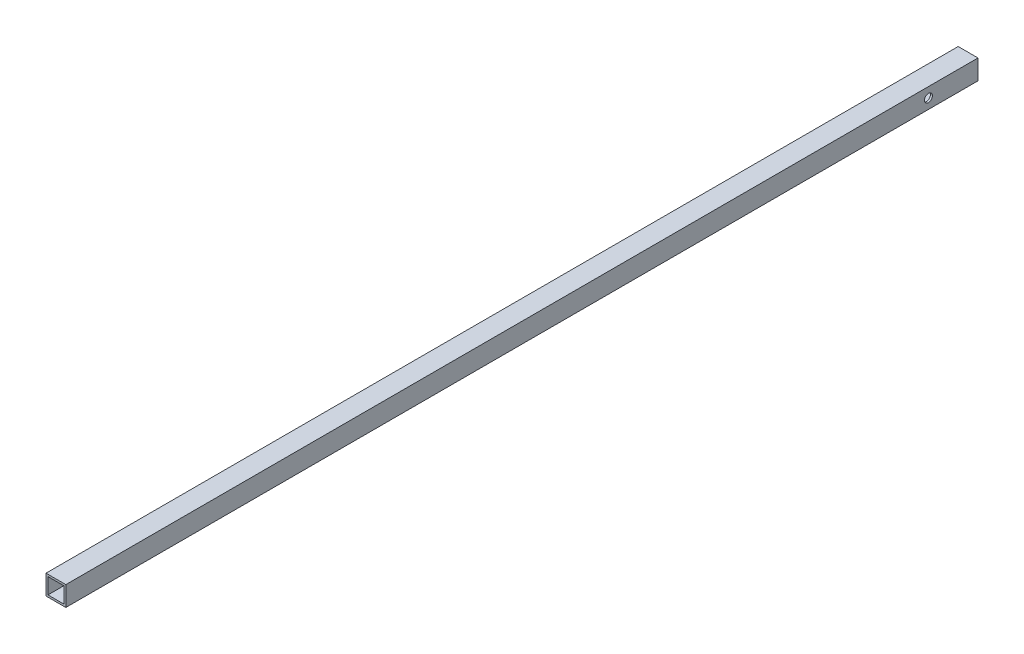
SolidWorks part; units mm, degrees
ref_plane "正面" through (0, 0, 0) normal (0, 0, 1) x (1, 0, 0)
ref_plane "平面" through (0, 0, 0) normal (0, 1, 0) x (1, 0, 0)
ref_plane "右側面" through (0, 0, 0) normal (1, 0, 0) x (0, 0, -1)
sketch "ｽｹｯﾁ1" plane through (0, 0, 0) normal (0, 0, 1) x (1, 0, 0)
  line L1 (-10, 10) -> (10, 10)
  line L2 (-10, 10) -> (-10, -10)
  line L3 (-10, -10) -> (10, -10)
  line L4 (10, 10) -> (10, -10)
  line L5 (-10, 10) -> (10, -10) construction
  line L6 (-10, -10) -> (10, 10) construction
  line L7 (-8, 8) -> (8, 8)
  line L8 (-8, 8) -> (-8, -8)
  line L9 (-8, -8) -> (8, -8)
  line L10 (8, 8) -> (8, -8)
  line L11 (-8, 8) -> (8, -8) construction
  line L12 (-8, -8) -> (8, 8) construction
  point P0 (0, 0)
  point P6 (0, 0)
  dimension "D1" = 20
  dimension "D2" = 20
  dimension "D3" = 16
  dimension "D4" = 16
extrude "ﾎﾞｽ - 押し出し1" add sketch "ｽｹｯﾁ1" along normal blind 970
sketch "ｽｹｯﾁ2" plane through (10, 0, 0) normal (1, 0, 0) x (0, 0, -1)
  line L0 (-970, 0) -> (-710, 0)
  line L1 (-970, -10) -> (-970, 10) construction
  line L2 (-710, 0) -> (-890.4665, 0)
  line L3 (-890.4665, 0) -> (-845.8821, 0)
  line L4 (-845.8821, 0) -> (-803.5394, 0)
  line L5 (-710, 0) -> (-670, 0)
  line L6 (-670, 0) -> (-50, 0)
  line L7 (-50, 0) -> (-40, 0)
  line L8 (-670, 0) -> (-650, 0)
  line L9 (-710, 0) -> (-730, 0)
  circle A0 centre (-710, 0) radius 1
  circle A4 centre (-670, 0) radius 2.2
  circle A5 centre (-50, 0) radius 4.05
  circle A6 centre (-40, 0) radius 1
  circle A7 centre (-650, 0) radius 2.1
  circle A8 centre (-730, 0) radius 1
  dimension "D5" = 2
  dimension "D6" = 8.1
  dimension "D7" = 4.4
  dimension "D8" = 2
  dimension "D10" = 4.2
  dimension "D12" = 2
  dimension "D1" = 260
  dimension "D2" = 40
  dimension "D3" = 620
  dimension "D4" = 10
  dimension "D9" = 20
  dimension "D11" = 20
extrude "ｶｯﾄ - 押し出し1" cut sketch "ｽｹｯﾁ2" against normal blind 970 contours L7 A5 L6 | L6 A5 L7 | A0
sketch "ｽｹｯﾁ3" plane through (0, 10, 0) normal (0, 1, 0) x (1, 0, 0)
  line L0 (0, -970) -> (0, -690)
  line L1 (10, -970) -> (-10, -970) construction
  line L2 (0, -690) -> (0, -670)
  line L3 (0, -670) -> (0, -10)
  line L4 (0, -670) -> (0, -650)
  line L5 (0, -650) -> (0, -630)
  circle A0 centre (0, -690) radius 2.1
  circle A1 centre (0, -670) radius 1
  circle A2 centre (0, -10) radius 2.2
  circle A3 centre (0, -650) radius 1
  circle A4 centre (0, -630) radius 2.1
  dimension "D2" = 4.2
  dimension "D4" = 2
  dimension "D6" = 4.4
  dimension "D7" = 2
  dimension "D9" = 4.2
  dimension "D1" = 280
  dimension "D3" = 20
  dimension "D5" = 20
  dimension "D8" = 20
sketch "ｽｹｯﾁ4" plane through (0, 0, 970) normal (0, 0, 1) x (1, 0, 0)
  line L1 (10.6881, 14.5445) -> (-10.6881, 14.5445)
  line L2 (10.6881, 14.5445) -> (10.6881, -14.5445)
  line L3 (10.6881, -14.5445) -> (-10.6881, -14.5445)
  line L4 (-10.6881, 14.5445) -> (-10.6881, -14.5445)
  line L5 (10.6881, 14.5445) -> (-10.6881, -14.5445) construction
  line L6 (10.6881, -14.5445) -> (-10.6881, 14.5445) construction
  point P0 (0, 0)
extrude "ｶｯﾄ - 押し出し3" cut sketch "ｽｹｯﾁ4" against normal blind 50
sketch "ｽｹｯﾁ5" plane through (10, 0, 0) normal (1, 0, 0) x (0, 0, -1)
  line L0 (-710, 0) -> (-816, 0)
  circle A0 centre (-816, 0) radius 2.2
  dimension "D2" = 4.4
  dimension "D1" = 106
sketch "ｽｹｯﾁ6" plane through (0, -10, 0) normal (0, -1, 0) x (1, 0, 0)
  line L0 (0, 0) -> (0, 30)
  line L1 (0, 30) -> (0, 50)
  circle A0 centre (0, 30) radius 1
  circle A1 centre (0, 50) radius 1
  dimension "D3" = 2
  dimension "D4" = 2
  dimension "D1" = 30
  dimension "D2" = 20
extrude "ｶｯﾄ - 押し出し5" cut sketch "ｽｹｯﾁ6" against normal blind 10
hole_wizard "M4x0.7 ねじ穴1" positions "3Dｽｹｯﾁ1" profile "ｽｹｯﾁ7" tap size "M4x0.7" standard "JIS"
sketch3d "3Dｽｹｯﾁ1"
  line L0 (0, -8, 30) -> (0, -10, 30) construction
  line L1 (0, -8, 50) -> (0, -10, 50) construction
  point P0 (0, -10, 30)
  point P4 (0, -10, 50)
cosmetic thread "穴のねじ山1" parameters "D1"=2, "D2"=4
cosmetic thread "穴のねじ山2" parameters "D1"=2, "D2"=4
sketch "ｽｹｯﾁ7" plane through (0, -10, 30) normal (1, 0, 0) x (0, 0, -1)
  line L0 (0, 0) -> (0, 5.9914)
  line L1 (0, 5.9914) -> (1.65, 5)
  line L2 (1.65, 5) -> (1.65, 0)
  line L5 (1.65, 0) -> (0, 0)
  line L10 (0, 5.9914) -> (-1.65, 5) construction
  line L11 (0, -6.35) -> (0, 107.95) construction
  dimension "ねじ下穴ﾄﾞﾘﾙ直径" = 3.3
  dimension "ねじ下穴ﾄﾞﾘﾙの深さ" = 5
  dimension "ﾄﾞﾘﾙ角度" = 118
sketch "ｽｹｯﾁ10" plane through (0, -10, 0) normal (0, -1, 0) x (-1, 0, 0)
  line L0 (0, -920) -> (0, -670)
  line L1 (-10, -920) -> (10, -920) construction
  line L2 (0, -670) -> (0, -650)
  circle A0 centre (0, -670) radius 1
  circle A1 centre (0, -650) radius 1
  dimension "D3" = 2
  dimension "D4" = 2
  dimension "D1" = 250
  dimension "D2" = 20
extrude "ｶｯﾄ - 押し出し6" cut sketch "ｽｹｯﾁ10" against normal blind 5
hole_wizard "M4x0.7 ねじ穴4" positions "3Dｽｹｯﾁ4" profile "ｽｹｯﾁ11" tap size "M4x0.7" standard "JIS"
sketch3d "3Dｽｹｯﾁ4"
  line L0 (0, -8, 650) -> (0, -10, 650) construction
  line L1 (0, -8, 670) -> (0, -10, 670) construction
  point P0 (0, -10, 650)
  point P4 (0, -8, 670)
sketch "ｽｹｯﾁ11" plane through (0, -10, 650) normal (1, 0, 0) x (0, 0, -1)
  line L0 (0, 0) -> (0, 5.9914)
  line L1 (0, 5.9914) -> (1.65, 5)
  line L2 (1.65, 5) -> (1.65, 0)
  line L5 (1.65, 0) -> (0, 0)
  line L10 (0, 5.9914) -> (-1.65, 5) construction
  line L11 (0, -6.35) -> (0, 107.95) construction
  dimension "ねじ下穴ﾄﾞﾘﾙ直径" = 3.3
  dimension "ねじ下穴ﾄﾞﾘﾙの深さ" = 5
  dimension "ﾄﾞﾘﾙ角度" = 118
cosmetic thread "穴のねじ山8" parameters "D1"=2, "D2"=4
cosmetic thread "穴のねじ山9" parameters "D1"=2, "D2"=4
sketch "ｽｹｯﾁ12" plane through (-10, 0, 0) normal (-1, 0, 0) x (0, 0, 1)
  line L0 (920, 0) -> (730, 0)
  line L1 (920, -10) -> (920, 10) construction
  line L2 (730, 0) -> (710, 0)
  line L3 (0, 10) -> (0, -10) construction
  line L4 (0, 0) -> (40, 0)
  circle A0 centre (710, 0) radius 1
  circle A1 centre (730, 0) radius 1
  circle A3 centre (40, 0) radius 1
  dimension "D3" = 2
  dimension "D4" = 2
  dimension "D5" = 2
  dimension "D1" = 190
  dimension "D2" = 20
  dimension "D6" = 40
extrude "ｶｯﾄ - 押し出し7" cut sketch "ｽｹｯﾁ12" against normal blind 5
hole_wizard "M4x0.7 ねじ穴5" positions "3Dｽｹｯﾁ5" profile "ｽｹｯﾁ13" tap size "M4x0.7" standard "JIS"
sketch3d "3Dｽｹｯﾁ5"
  line L0 (-8, 0, 730) -> (-10, 0, 730) construction
  line L1 (-8, 0, 710) -> (-10, 0, 710) construction
  line L2 (-8, 0, 40) -> (-10, 0, 40) construction
  point P0 (-10, 0, 730)
  point P4 (-10, 0, 710)
  point P8 (-8, 0, 40)
sketch "ｽｹｯﾁ13" plane through (-10, 0, 730) normal (0, 1, 0) x (0, 0, 1)
  line L0 (0, 0) -> (0, 9.9914)
  line L1 (0, 9.9914) -> (1.65, 9)
  line L2 (1.65, 9) -> (1.65, 0)
  line L5 (1.65, 0) -> (0, 0)
  line L10 (0, 9.9914) -> (-1.65, 9) construction
  line L11 (0, -6.35) -> (0, 107.95) construction
  dimension "ねじ下穴ﾄﾞﾘﾙ直径" = 3.3
  dimension "ねじ下穴ﾄﾞﾘﾙの深さ" = 9
  dimension "ﾄﾞﾘﾙ角度" = 118
cosmetic thread "穴のねじ山10" parameters "D1"=2, "D2"=4
cosmetic thread "穴のねじ山11" parameters "D1"=2, "D2"=4
cosmetic thread "穴のねじ山12" parameters "D1"=2, "D2"=4
